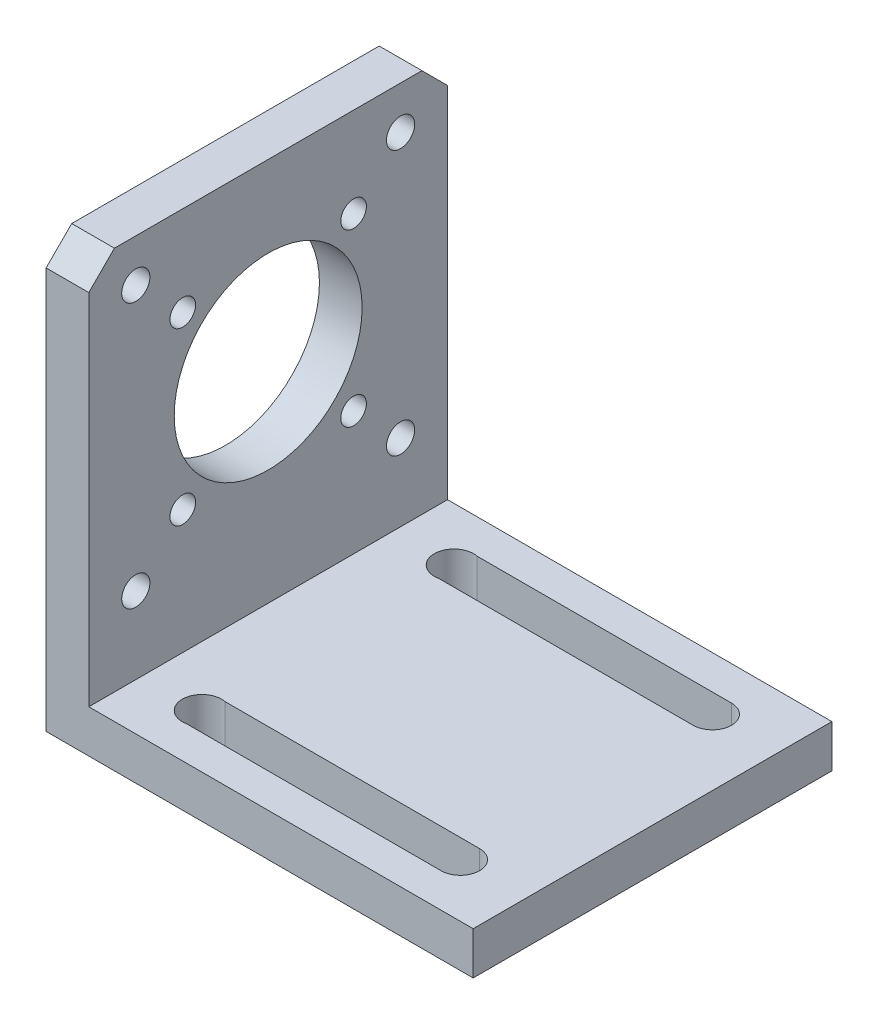
SolidWorks part; units mm, degrees
ref_plane "Front Plane" through (0, 0, 0) normal (0, 0, 1) x (1, 0, 0)
ref_plane "Top Plane" through (0, 0, 0) normal (0, 1, 0) x (1, 0, 0)
ref_plane "Right Plane" through (0, 0, 0) normal (1, 0, 0) x (0, 0, -1)
sketch "Sketch1" plane through (0, 0, 0) normal (0, 1, 0) x (1, 0, 0)
  line L1 (0, 0) -> (50, 0)
  line L2 (0, 0) -> (0, 42)
  line L3 (0, 42) -> (50, 42)
  line L4 (50, 0) -> (50, 42)
  dimension "D1" = 50
  dimension "D2" = 42
extrude "Boss-Extrude1" add sketch "Sketch1" along normal blind 5
sketch "Sketch2" plane through (0, 5, 0) normal (0, 1, 0) x (1, 0, 0)
  line L0 (50, 42) -> (0, 42) construction
  line L1 (0, 0) -> (5, 0)
  line L2 (0, 0) -> (0, 42)
  line L3 (0, 42) -> (5, 42)
  line L4 (5, 0) -> (5, 42)
  dimension "D1" = 5
extrude "Boss-Extrude2" add sketch "Sketch2" along normal blind 45
sketch "Sketch3" plane through (5, 0, 0) normal (1, 0, 0) x (0, 0, -1)
  line L0 (0, 47) -> (3, 50)
  line L1 (0, 50) -> (0, 5) construction
  line L2 (0, 50) -> (42, 50) construction
  line L3 (3, 50) -> (0, 50)
  line L4 (0, 50) -> (0, 47)
  line L5 (42, 50) -> (39, 50)
  line L6 (39, 50) -> (42, 47)
  line L7 (42, 50) -> (42, 5) construction
  line L8 (42, 47) -> (42, 50)
  dimension "D1" = 3
  dimension "D2" = 3
  dimension "D3" = 3
  dimension "D4" = 3
extrude "Cut-Extrude1" cut sketch "Sketch3" against normal blind 45
sketch "Sketch4" plane through (0, 5, 0) normal (0, 1, 0) x (1, 0, 0)
  line L0 (5, 0) -> (50, 0) construction
  line L1 (5, 0) -> (5, 42) construction
  line L2 (12.4716, 8.5) -> (42.25, 8.5)
  line L3 (42.25, 4) -> (12.4716, 4)
  line L4 (50, 0) -> (50, 42) construction
  line L5 (12.4716, 38) -> (42.25, 38)
  line L6 (42.25, 33.5) -> (12.4716, 33.5)
  arc A0 (12.4716, 8.5) -> (12.4716, 4) centre (12, 6.25) ccw
  arc A1 (42.25, 8.5) -> (42.25, 4) centre (42.25, 6.25) cw
  arc A2 (42.25, 38) -> (42.25, 33.5) centre (42.25, 35.75) cw
  arc A3 (12.4716, 38) -> (12.4716, 33.5) centre (12, 35.75) ccw
  dimension "D3" = 7
  dimension "D4" = 7.75
  dimension "D1" = 4
  dimension "D2" = 4.5
  dimension "D5" = 4.5
  dimension "D7" = 29.5
  dimension "D6" = 2
extrude "Cut-Extrude3" cut sketch "Sketch4" against normal through all contours L2 A1 L3 A0 | L6 A3 L5 A2
sketch "Sketch7" plane through (5, 0, 0) normal (1, 0, 0) x (0, 0, -1)
  line L0 (42, 47) -> (42, 5) construction
  line L1 (3, 50) -> (39, 50) construction
  circle A0 centre (21, 29.5) radius 11
  circle A1 centre (5.5, 45) radius 1.65
  circle A2 centre (31, 39.5) radius 1.5
  circle A3 centre (5.5, 14) radius 1.65
  circle A4 centre (31, 19.5) radius 1.5
  circle A5 centre (36.5, 14) radius 1.65
  circle A6 centre (11, 19.5) radius 1.5
  circle A8 centre (11, 39.5) radius 1.5
  circle A12 centre (36.5, 45) radius 1.65
  point P24 (21, 29.5)
  point P36 (21, 29.5)
  dimension "D1" = 22
  dimension "D4" = 3
  dimension "D5" = 3.3
  dimension "D6" = 10
  dimension "D2" = 21
  dimension "D3" = 20.5
  dimension "D7" = 10
  dimension "D8" = 10
  dimension "D9" = 10
  dimension "D10" = 15.5
  dimension "D11" = 15.5
  dimension "D12" = 15.5
  dimension "D13" = 15.5
extrude "Cut-Extrude4" cut sketch "Sketch7" against normal through all
